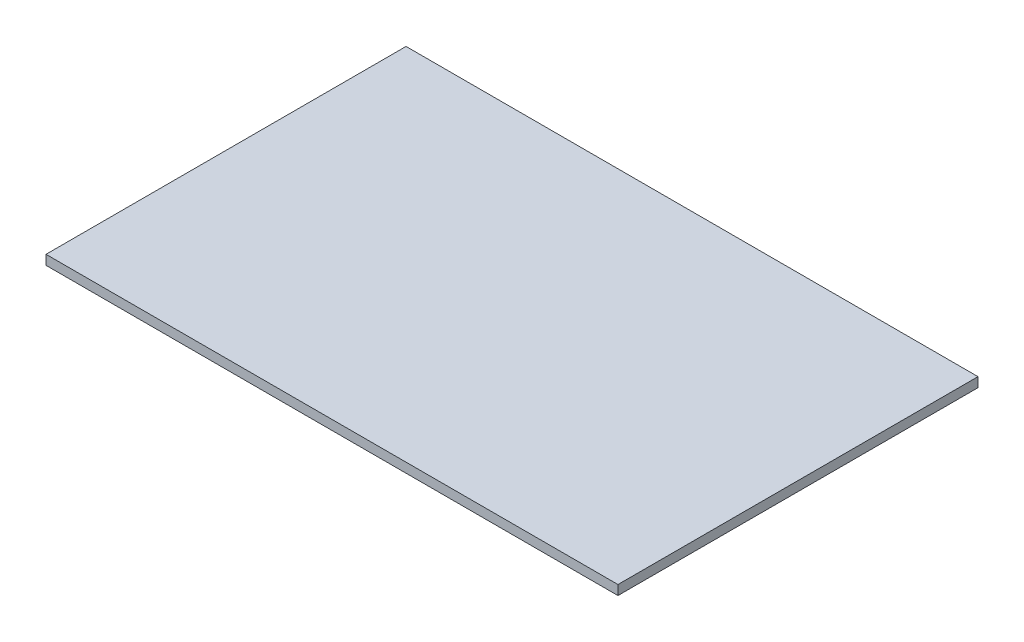
SolidWorks part; units mm, degrees
ref_plane "Plano frontal" through (0, 0, 0) normal (0, 0, 1) x (1, 0, 0)
ref_plane "Plano superior" through (0, 0, 0) normal (0, 1, 0) x (1, 0, 0)
ref_plane "Plano direito" through (0, 0, 0) normal (1, 0, 0) x (0, 0, -1)
sketch "Esboço2" plane through (0, 0, 0) normal (0, 1, 0) x (1, 0, 0)
  line L1 (-895, -563.4) -> (895, -563.4)
  line L2 (-895, -563.4) -> (-895, 563.4)
  line L3 (-895, 563.4) -> (895, 563.4)
  line L4 (895, -563.4) -> (895, 563.4)
  line L5 (-895, -563.4) -> (895, 563.4) construction
  line L6 (-895, 563.4) -> (895, -563.4) construction
  point P0 (0, 0)
  dimension "D1" = 1126.8
  dimension "D2" = 1790
extrude "Ressalto-extrusão1" add sketch "Esboço2" along normal blind 30
